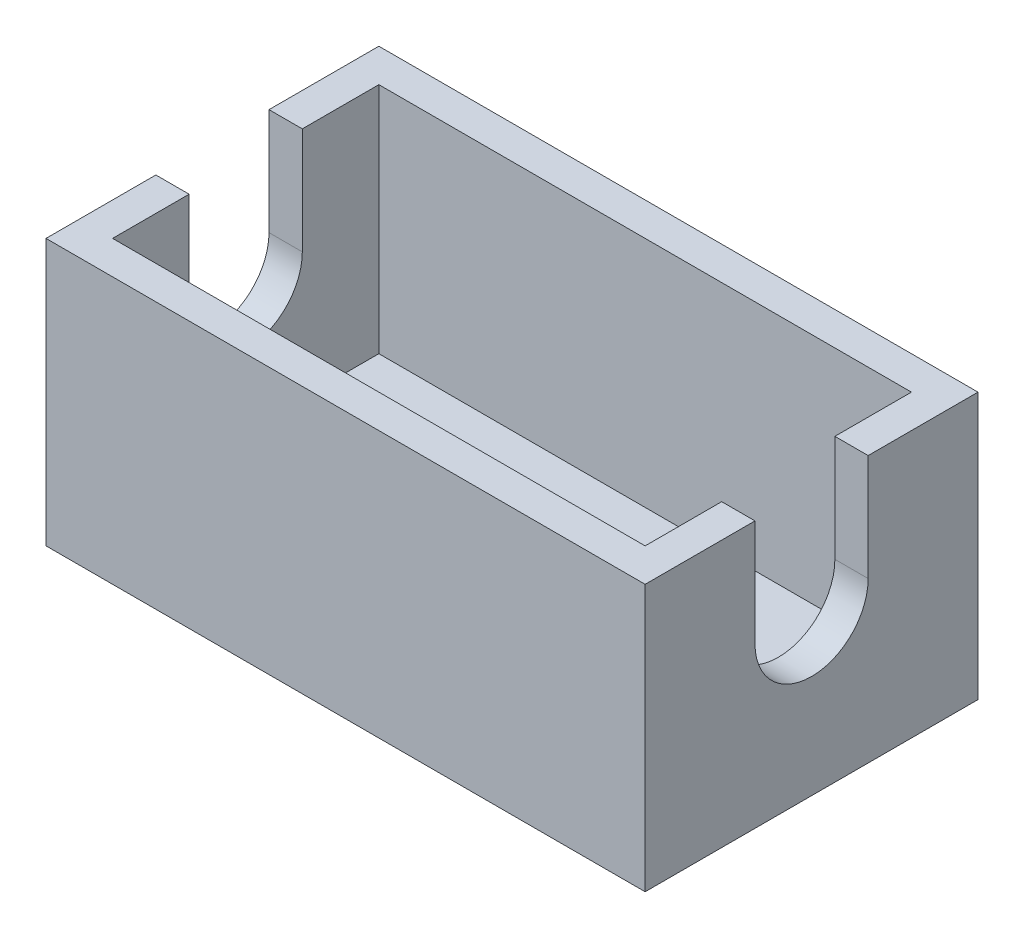
SolidWorks part; units mm, degrees
ref_plane "Front Plane" through (0, 0, 0) normal (0, 0, 1) x (1, 0, 0)
ref_plane "Top Plane" through (0, 0, 0) normal (0, 1, 0) x (1, 0, 0)
ref_plane "Right Plane" through (0, 0, 0) normal (1, 0, 0) x (0, 0, -1)
sketch "Sketch1" plane through (0, 0, 0) normal (0, 1, 0) x (1, 0, 0)
  line L1 (22.5, -12.5) -> (-22.5, -12.5)
  line L2 (22.5, -12.5) -> (22.5, 12.5)
  line L3 (22.5, 12.5) -> (-22.5, 12.5)
  line L4 (-22.5, -12.5) -> (-22.5, 12.5)
  line L5 (22.5, -12.5) -> (-22.5, 12.5) construction
  line L6 (22.5, 12.5) -> (-22.5, -12.5) construction
  point P0 (0, 0)
  dimension "D1" = 45
  dimension "D2" = 25
extrude "Boss-Extrude1" add sketch "Sketch1" along normal blind 2.5
sketch "Sketch2" plane through (0, 2.5, 0) normal (0, 1, 0) x (1, 0, 0)
  line L0 (22.5, 12.5) -> (-22.5, 12.5) construction
  line L1 (20, -10) -> (-20, -10)
  line L2 (20, -10) -> (20, 10)
  line L3 (20, 10) -> (-20, 10)
  line L4 (-20, -10) -> (-20, 10)
  line L5 (20, -10) -> (-20, 10) construction
  line L6 (20, 10) -> (-20, -10) construction
  line L7 (-22.5, 12.5) -> (-22.5, -12.5) construction
  line L9 (22.5, -12.5) -> (-22.5, -12.5)
  line L10 (22.5, -12.5) -> (22.5, 12.5)
  line L11 (22.5, 12.5) -> (-22.5, 12.5)
  line L12 (-22.5, -12.5) -> (-22.5, 12.5)
  line L13 (22.5, -12.5) -> (-22.5, 12.5) construction
  line L14 (22.5, 12.5) -> (-22.5, -12.5) construction
  point P0 (0, 0)
  point P10 (0, 0)
  dimension "D1" = 2.5
  dimension "D2" = 2.5
extrude "Boss-Extrude2" add sketch "Sketch2" along normal blind 17.5
sketch "Sketch3" plane through (22.5, 0, 0) normal (1, 0, 0) x (0, 0, -1)
  line L0 (0, 12) -> (0, 0) construction
  line L2 (-4.25, 12) -> (-4.25, 20)
  line L3 (-12.5, 20) -> (12.5, 20) construction
  line L4 (-4.25, 20) -> (4.25, 20)
  line L5 (4.25, 20) -> (4.25, 12)
  arc A0 (-4.25, 12) -> (4.25, 12) centre (0, 12) ccw
  dimension "D1" = 8.5
  dimension "D2" = 12
extrude "Cut-Extrude1" cut sketch "Sketch3" against normal through all
